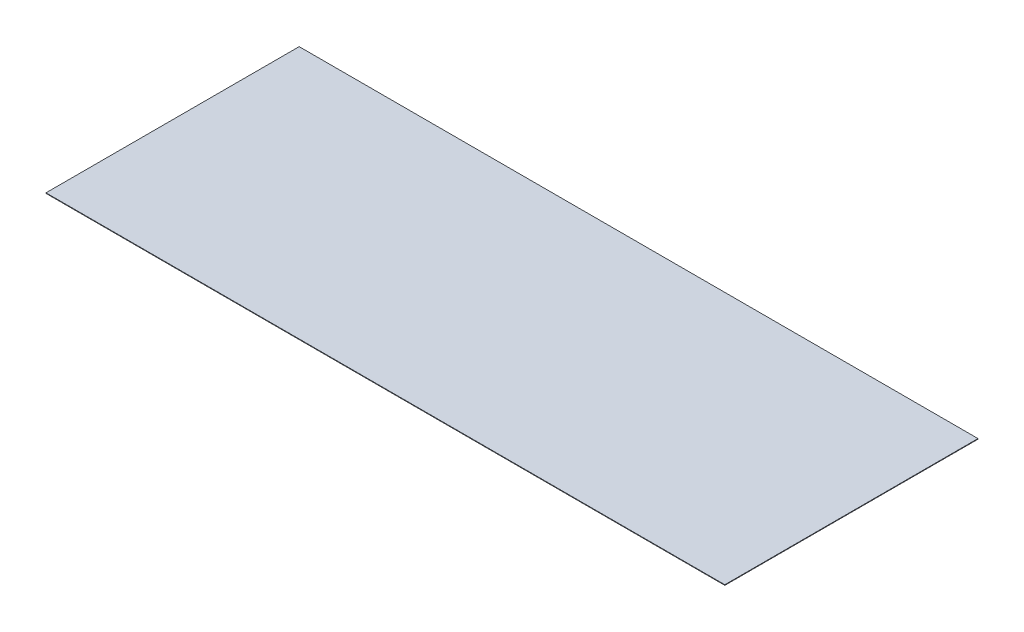
SolidWorks part; units mm, degrees
ref_plane "Alzado" through (0, 0, 0) normal (0, 0, 1) x (1, 0, 0)
ref_plane "Planta" through (0, 0, 0) normal (0, 1, 0) x (1, 0, 0)
ref_plane "Vista lateral" through (0, 0, 0) normal (1, 0, 0) x (0, 0, -1)
sketch "Croquis1" plane through (0, 0, 0) normal (0, 1, 0) x (1, 0, 0)
  line L1 (-1220, 455) -> (1220, 455)
  line L2 (-1220, 455) -> (-1220, -455)
  line L3 (-1220, -455) -> (1220, -455)
  line L4 (1220, 455) -> (1220, -455)
  line L5 (-1220, 455) -> (1220, -455) construction
  line L6 (-1220, -455) -> (1220, 455) construction
  point P0 (0, 0)
  dimension "D1" = 910
  dimension "D2" = 2440
extrude "Saliente-Extruir1" add sketch "Croquis1" along normal blind 2
sketch "Croquis2" plane through (0, 2, 0) normal (0, 1, 0) x (1, 0, 0)
  line L0 (1220, 455) -> (-1220, 455) construction
  line L1 (-626.8185, -228.4) -> (-432.4247, 108.3)
  line L2 (-432.4247, 108.3) -> (-626.8185, 445)
  line L3 (-626.8185, 445) -> (-1015.6062, 445)
  line L4 (-1015.6062, 445) -> (-1210, 108.3)
  line L5 (-1210, 108.3) -> (-1015.6062, -228.4)
  line L6 (-1015.6062, -228.4) -> (-626.8185, -228.4)
  line L7 (-1220, 455) -> (-1220, -455) construction
  line L9 (-1220, -455) -> (1220, -455) construction
  line L10 (-1210, 445) -> (-432.4247, 445)
  line L11 (-1210, 445) -> (-1210, -228.4)
  line L12 (-1210, -228.4) -> (-432.4247, -228.4)
  line L13 (-432.4247, 445) -> (-432.4247, -228.4)
  line L14 (-1210, 445) -> (-432.4247, -228.4) construction
  line L15 (-1210, -228.4) -> (-432.4247, 445) construction
  line L16 (-1220, -305) -> (1200, -305)
  line L17 (-1220, -305) -> (-1220, -455)
  line L18 (-1220, -455) -> (1200, -455)
  line L19 (1200, -305) -> (1200, -455)
  line L26 (219.463, -250) -> (420.0922, 97.5)
  line L27 (420.0922, 97.5) -> (219.463, 445)
  line L28 (219.463, 445) -> (-181.7954, 445)
  line L29 (-181.7954, 445) -> (-382.4247, 97.5)
  line L30 (-382.4247, 97.5) -> (-181.7954, -250)
  line L31 (-181.7954, -250) -> (219.463, -250)
  line L33 (-382.4247, 445) -> (420.0922, 445)
  line L34 (-382.4247, 445) -> (-382.4247, -250)
  line L35 (-382.4247, -250) -> (420.0922, -250)
  line L36 (420.0922, 445) -> (420.0922, -250)
  line L37 (-382.4247, 445) -> (420.0922, -250) construction
  line L38 (-382.4247, -250) -> (420.0922, 445) construction
  circle A0 centre (-821.2123, 108.3) radius 336.7 construction
  circle A1 centre (18.8338, 97.5) radius 347.5 construction
  dimension "D1" = 673.4
  dimension "D7" = 50
  dimension "D6" = 695
  dimension "D2" = 10
  dimension "D3" = 10
  dimension "D4" = 150
  dimension "D5" = 2420
  dimension "D8" = 55
